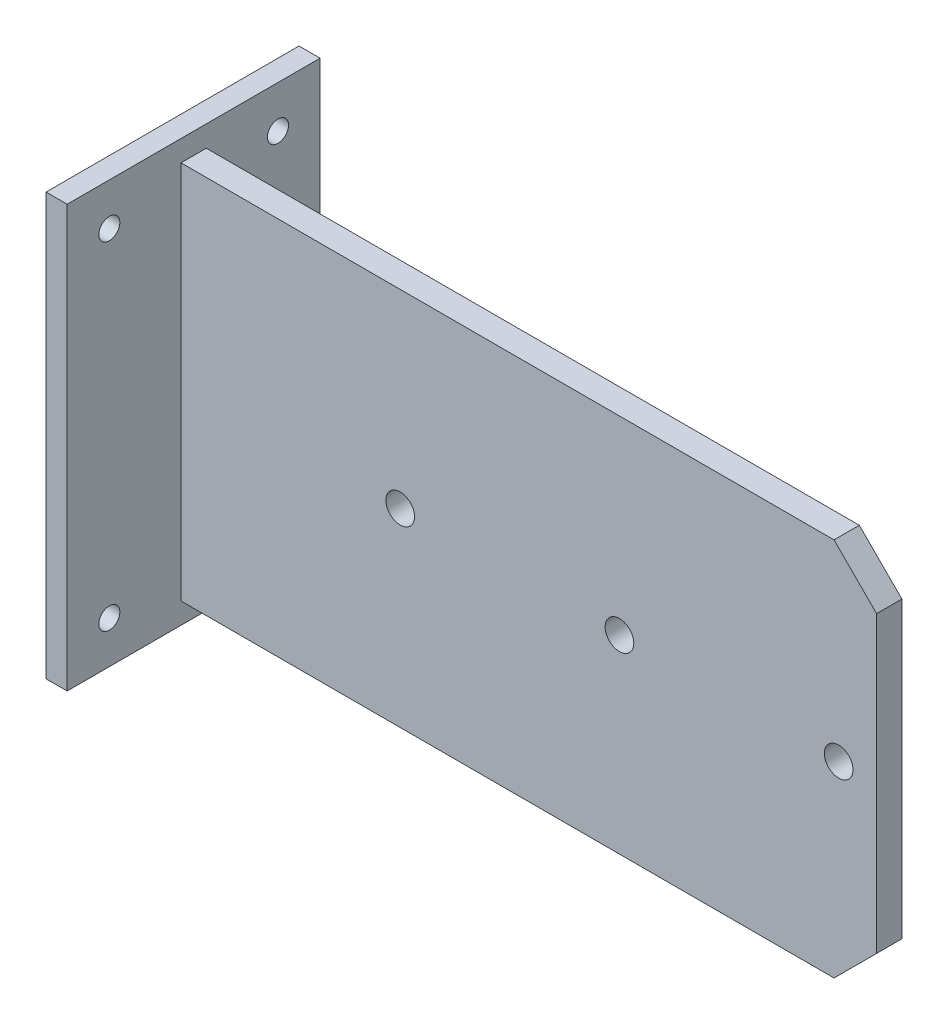
SolidWorks part; units mm, degrees
ref_plane "Front Plane" through (0, 0, 0) normal (0, 0, 1) x (1, 0, 0)
ref_plane "Top Plane" through (0, 0, 0) normal (0, 1, 0) x (1, 0, 0)
ref_plane "Right Plane" through (0, 0, 0) normal (1, 0, 0) x (0, 0, -1)
sketch "Sketch1" plane through (0, 0, 0) normal (0, 0, 1) x (1, 0, 0)
  line L1 (63.5, -1270) -> (-63.5, -1270)
  line L2 (63.5, -1270) -> (63.5, 1270)
  line L3 (63.5, 1270) -> (-63.5, 1270)
  line L4 (-63.5, -1270) -> (-63.5, 1270)
  line L5 (63.5, -1270) -> (-63.5, 1270) construction
  line L6 (63.5, 1270) -> (-63.5, -1270) construction
  point P0 (0, 0)
  dimension "D1" = 2540
  dimension "D2" = 127
extrude "Boss-Extrude1" add sketch "Sketch1" along normal mid plane 1524
ref_plane "Plane1" through (0, 0, 0) normal (0, 0, 1) x (1, 0, 0)
sketch "Sketch2" plane through (0, 0, 0) normal (0, 0, 1) x (1, 0, 0)
  line L0 (63.5, 0) -> (4254.5, 0) construction
  line L1 (63.5, -1270) -> (63.5, 1270) construction
  line L2 (-63.5, 1270) -> (-63.5, -1270) construction
  line L3 (63.5, 1143) -> (4254.5, 1143)
  line L4 (63.5, -1143) -> (4254.5, -1143)
  line L5 (4254.5, 1143) -> (4254.5, -1143)
  line L6 (63.5, -1143) -> (63.5, 1143)
  dimension "D1" = 4318
  dimension "D2" = 1143
extrude "Boss-Extrude2" add sketch "Sketch2" along normal mid plane 152.4 contours L3 L5 L4 L6
sketch "Sketch3" plane through (-63.5, 0, 0) normal (-1, 0, 0) x (0, 0, 1)
  line L1 (0, 1270) -> (0, -1270) construction
  line L2 (762, 1270) -> (-762, 1270) construction
  line L3 (762, -1270) -> (-762, -1270) construction
  circle A0 centre (-508, 1016) radius 63.5
  circle A1 centre (-508, -1016) radius 63.5
  circle A2 centre (508, -1016) radius 63.5
  circle A3 centre (508, 1016) radius 63.5
  dimension "D1" = 127
  dimension "D3" = 2032
  dimension "D4" = 508
  dimension "D2" = 1016
extrude "Cut-Extrude1" cut sketch "Sketch3" against normal blind 152.4
sketch "Sketch4" plane through (0, 0, 76.2) normal (0, 0, 1) x (1, 0, 0)
  line L0 (63.5, -1143) -> (4254.5, -1143) construction
  line L1 (4254.5, 1143) -> (4254.5, -1143) construction
  circle A0 centre (4025.9, 0) radius 86.36
  circle A1 centre (2705.1, 0) radius 86.36
  circle A2 centre (1384.3, 0) radius 86.36
  dimension "D1" = 172.72
  dimension "D2" = 1143
  dimension "D3" = 228.6
  dimension "D4" = 1320.8
  dimension "D5" = 1320.8
extrude "Cut-Extrude2" cut sketch "Sketch4" against normal through all
chamfer "Chamfer1" distance 256.54 2 edges at (4254.5, -1143, 0) (4254.5, 1143, 0)
